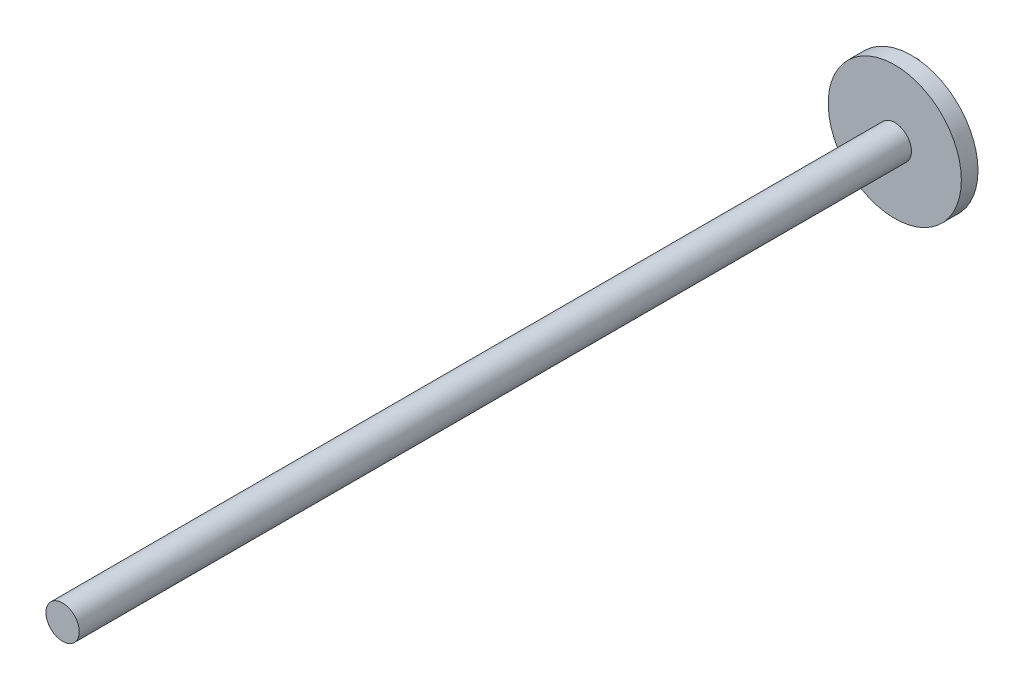
SolidWorks part; units mm, degrees
ref_plane "Front Plane" through (0, 0, 0) normal (0, 0, 1) x (1, 0, 0)
ref_plane "Top Plane" through (0, 0, 0) normal (0, 1, 0) x (1, 0, 0)
ref_plane "Right Plane" through (0, 0, 0) normal (1, 0, 0) x (0, 0, -1)
sketch "Sketch1" plane through (0, 0, 0) normal (0, 0, 1) x (1, 0, 0)
  circle A0 centre (0, 0) radius 40
  dimension "D1" = 80
extrude "Boss-Extrude1" add sketch "Sketch1" along normal blind 10
sketch "Sketch2" plane through (0, 0, 10) normal (0, 0, 1) x (1, 0, 0)
  circle A0 centre (0, 0) radius 10
extrude "Boss-Extrude2" add sketch "Sketch2" along normal blind 500
cosmetic thread "Cosmetic Thread2" parameters "D1"=450, "D2"=17.252
sketch "Sketch3" plane through (0, 0, 0) normal (0, 0, -1) x (-1, 0, 0)
  circle A0 centre (26.9986, 0) radius 10
extrude "Boss-Extrude3" add sketch "Sketch3" along normal blind 30
